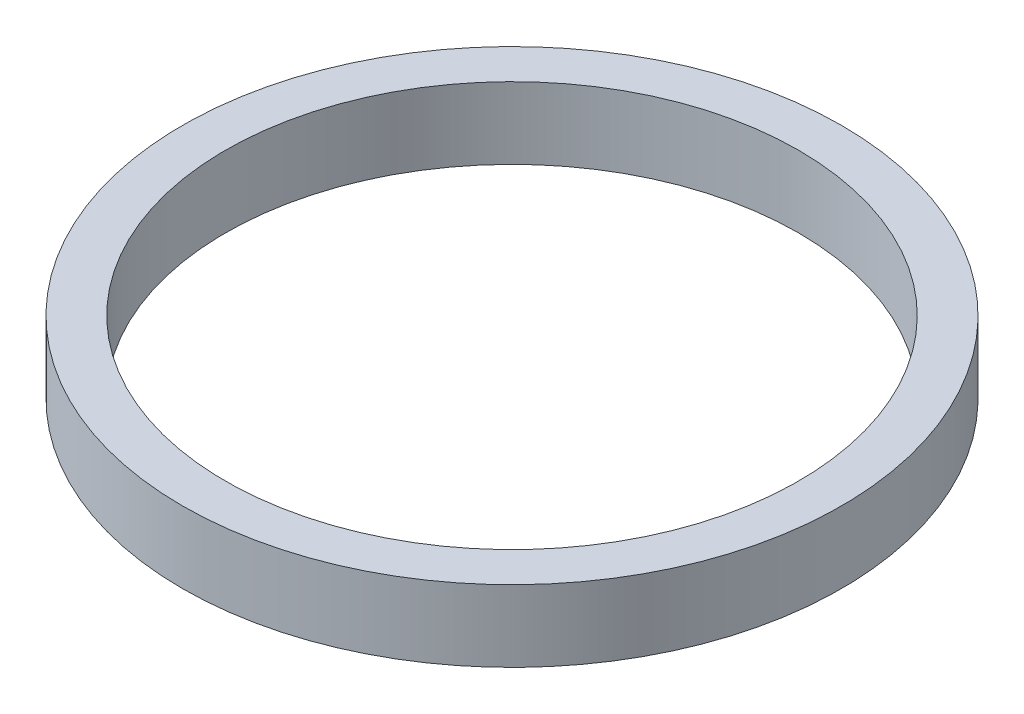
SolidWorks part; units mm, degrees
ref_plane "Спереди" through (0, 0, 0) normal (0, 0, 1) x (1, 0, 0)
ref_plane "Сверху" through (0, 0, 0) normal (0, 1, 0) x (1, 0, 0)
ref_plane "Справа" through (0, 0, 0) normal (1, 0, 0) x (0, 0, -1)
sketch "Эскиз1" plane through (0, 0, 0) normal (0, 0, 1) x (1, 0, 0)
  line L0 (10, 0) -> (10, 2.5)
  line L1 (10, 2.5) -> (11.5, 2.5)
  line L2 (11.5, 2.5) -> (11.5, 0)
  line L3 (11.5, 0) -> (10, 0)
  line L4 (0, 0) -> (0, 3.3903) construction
  dimension "D1" = 10
  dimension "D2" = 11.5
  dimension "D3" = 2.5
revolve "Повернуть1" add sketch "Эскиз1" angle 360 about L4
